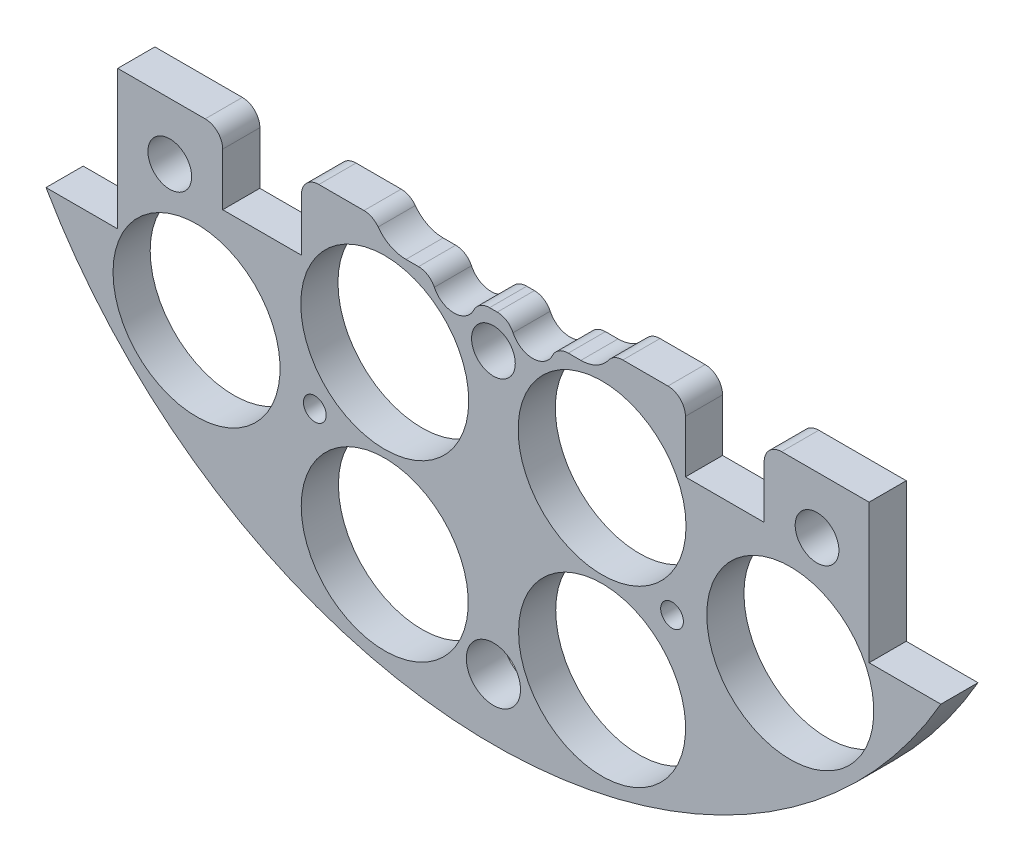
SolidWorks part; units mm, degrees
ref_plane "Front Plane" through (0, 0, 0) normal (0, 0, 1) x (1, 0, 0)
ref_plane "Top Plane" through (0, 0, 0) normal (0, 1, 0) x (1, 0, 0)
ref_plane "Right Plane" through (0, 0, 0) normal (1, 0, 0) x (0, 0, -1)
sketch "Sketch1" plane through (0, 0, 0) normal (0, 0, 1) x (1, 0, 0)
  line L0 (0, 0) -> (-82.1241, 0) construction
  line L1 (0, 0) -> (0, 95.6219) construction
  line L3 (-64.9644, 37.338) -> (-54.5504, 37.338)
  line L5 (-64.9644, -37.338) -> (-54.5504, -37.338)
  line L6 (-54.5504, 37.338) -> (-54.5504, -37.338)
  line L7 (64.9644, -37.338) -> (54.5504, -37.338)
  line L8 (64.9644, 37.338) -> (54.5504, 37.338)
  line L9 (54.5504, 37.338) -> (54.5504, -37.338)
  arc A0 (-64.9644, -37.338) -> (64.9644, -37.338) centre (0, 0) ccw
  circle A1 centre (-46.482, 11.049) radius 1.651
  circle A2 centre (-21.0833, 10.795) radius 1.651
  circle A3 centre (-21.0833, -10.795) radius 1.651
  circle A4 centre (-46.482, -11.049) radius 1.651
  circle A5 centre (46.482, -11.049) radius 1.651
  circle A6 centre (21.0833, -10.795) radius 1.651
  circle A7 centre (21.0833, 10.795) radius 1.651
  circle A8 centre (46.482, 11.049) radius 1.651
  arc A9 (64.9644, 37.338) -> (-64.9644, 37.338) centre (0, 0) ccw
  dimension "D2" = 3.302
  dimension "D3" = 3.302
  dimension "D4" = 25.4
  dimension "D5" = 10.795
  dimension "D10" = 46.482
  dimension "D6" = 74.676
  dimension "D7" = 10.414
  dimension "D8" = 74.93
  dimension "D9" = 74.93
  dimension "D11" = 37.338
extrude "Boss-Extrude2" add sketch "Sketch1" along normal blind 5.3975
sketch "Sketch2" plane through (0, 0, 5.3975) normal (0, 0, 1) x (1, 0, 0)
  line L0 (0, 68.58) -> (0, 55.88) construction
  line L1 (-9.525, 68.58) -> (9.525, 68.58)
  line L2 (-9.525, 68.58) -> (-9.525, 55.88)
  line L3 (-9.525, 55.88) -> (9.525, 55.88)
  line L4 (9.525, 68.58) -> (9.525, 55.88)
  line L5 (-9.525, 62.23) -> (9.525, 62.23) construction
  arc A0 (64.9644, 37.338) -> (-64.9644, 37.338) centre (0, 0) ccw construction
  circle A1 centre (-21.0833, 10.795) radius 1.651 construction
  circle A2 centre (21.0833, 10.795) radius 1.651 construction
  circle A3 centre (-6.731, 62.23) radius 1.143
  circle A4 centre (6.731, 62.23) radius 1.143
  dimension "D4" = 2.286
  dimension "D5" = 0
  dimension "D6" = 6.731
  dimension "D1" = 19.05
  dimension "D2" = 12.7
  dimension "D3" = 55.88
extrude "Cut-Extrude1" cut sketch "Sketch2" against normal through all contours A3 | A4
sketch "Sketch3" plane through (0, 0, 0) normal (0, 0, -1) x (-1, 0, 0)
  line L0 (0, 0) -> (0, -116.2908) construction
  line L1 (0, 0) -> (-153.8039, 0) construction
  line L2 (0, 0) -> (15.2681, -56.9814) construction
  line L3 (0, 0) -> (15.2302, -26.3795) construction
  circle A0 centre (-15.7776, -58.8828) radius 12.1285
  circle A3 centre (15.7776, -58.8828) radius 12.1285
  circle A4 centre (-43.1052, -43.1052) radius 12.1285
  circle A8 centre (-43.1052, 43.1052) radius 12.1285
  circle A11 centre (43.1052, 43.1052) radius 12.1285
  circle A14 centre (43.1052, -43.1052) radius 12.1285
  circle A33 centre (58.8828, -15.7776) radius 12.1285 [skipped]
  circle A34 centre (58.8828, 15.7776) radius 12.1285 [skipped]
  circle A35 centre (-58.8828, 15.7776) radius 12.1285 [skipped]
  circle A36 centre (-58.8828, -15.7776) radius 12.1285 [skipped]
  circle A37 centre (-15.7776, 58.8828) radius 12.1285 [skipped]
  circle A38 centre (15.7776, 58.8828) radius 12.1285 [skipped]
  point P36 (0, 0)
  point P53 (0, 0)
  point P55 (0, 0)
  dimension "D3" = 0
  dimension "D4" = 15
  dimension "D5" = 24.257
  dimension "D7" = 12
  dimension "D9" = 30
extrude "Cut-Extrude2" cut sketch "Sketch3" against normal through all
sketch "Sketch4" plane through (0, 0, 0) normal (0, 0, -1) x (-1, 0, 0)
  line L1 (-15.7702, 56.3138) -> (12.7925, 56.3138)
  line L2 (-15.7702, 56.3138) -> (-15.7702, 67.9913)
  line L3 (-15.7702, 67.9913) -> (12.7925, 67.9913)
  line L4 (12.7925, 56.3138) -> (12.7925, 67.9913)
extrude "Boss-Extrude3" add sketch "Sketch4" against normal up to surface (5.3975 mm away) up to face at (-55.2337, -43.1052, 5.3975)
sketch "Sketch5" plane through (0, 0, 0) normal (0, 0, -1) x (-1, 0, 0)
  line L1 (-85.044, -17.145) -> (131.6774, -17.145)
  line L2 (-85.044, -17.145) -> (-85.044, 113.4242)
  line L3 (-85.044, 113.4242) -> (131.6774, 113.4242)
  line L4 (131.6774, -17.145) -> (131.6774, 113.4242)
  circle A0 centre (-21.0833, -10.795) radius 1.651 construction
  dimension "D1" = 6.35
extrude "Cut-Extrude4" cut sketch "Sketch5" against normal through all contours L2 L3 L4 L1
extrude "Cut-Extrude5" cut sketch "Sketch6" against normal through all both and the other way through all
sketch "Sketch6" plane through (31.3134, 132.614, -3.175) normal (0, 0, -1) x (0, 1, 0)
  line L0 (-132.614, -31.3134) -> (-132.614, 57.8454) construction
  line L1 (-132.614, -31.3134) -> (-222.516, -31.3134) construction
  circle A0 centre (-158.014, 14.4066) radius 3.175
  circle A1 centre (-173.254, -31.3134) radius 3.175
  circle A3 centre (-158.014, -77.0334) radius 3.175
  circle A4 centre (-107.214, -77.0334) radius 3.175
  circle A5 centre (-91.974, -31.3134) radius 3.175
  circle A6 centre (-107.214, 14.4066) radius 3.175
extrude "Cut-Extrude7" cut sketch "Sketch8" against normal blind 29.21
sketch "Sketch8" plane through (31.3134, 132.559, 0) normal (0, 0, -1) x (0, 1, 0)
  line L0 (-132.559, -31.3134) -> (6.1626, -31.3134) construction
  line L2 (-132.559, -31.3134) -> (-132.559, -122.6589) construction
  circle A0 centre (-190.979, 2.9766) radius 1.651
  circle A2 centre (-154.784, -31.3134) radius 1.651
  circle A3 centre (-190.979, -65.6034) radius 1.651
  circle A4 centre (-110.334, -31.3134) radius 1.651
  circle A5 centre (-74.139, -65.6034) radius 1.651
  circle A6 centre (-74.139, 2.9766) radius 1.651
sketch "Sketch11" plane through (0, 0, 0) normal (0, 0, -1) x (-1, 0, 0)
  line L0 (-54.5504, -17.145) -> (54.5504, -17.145) construction
  circle A0 centre (0, -66.045) radius 3.937
  point P4 (0, -17.145)
  dimension "D1" = 7.874
  dimension "D2" = 48.9
extrude "Cut-Extrude11" cut sketch "Sketch11" against normal through all
sketch "Sketch12" plane through (0, 0, 0) normal (0, 0, -1) x (-1, 0, 0)
  line L0 (-54.5504, -17.145) -> (54.5504, -17.145) construction
  line L1 (-39.3104, -17.145) -> (-27.8804, -17.145)
  line L2 (-39.3104, -17.145) -> (-39.3104, -27.305)
  line L3 (-39.3104, -27.305) -> (-27.8804, -27.305)
  line L4 (-27.8804, -17.145) -> (-27.8804, -27.305)
  line L5 (-54.5504, -37.338) -> (-54.5504, -17.145) construction
  line L6 (27.8804, -17.145) -> (39.3104, -17.145)
  line L7 (27.8804, -17.145) -> (27.8804, -27.305)
  line L8 (27.8804, -27.305) -> (39.3104, -27.305)
  line L9 (39.3104, -17.145) -> (39.3104, -27.305)
  line L10 (0, -10.2409) -> (0, -88.0539) construction
  dimension "D1" = 15.24
  dimension "D2" = 11.43
  dimension "D3" = 10.16
extrude "Cut-Extrude12" cut sketch "Sketch12" against normal through all
sketch "Sketch16" plane through (0, 0, 0) normal (0, 0, -1) x (-1, 0, 0)
  line L0 (0, 0) -> (0, 27.5884) construction
  circle A0 centre (15.7776, -33.4828) radius 12.192
  circle A2 centre (15.7776, -58.8828) radius 12.1285 construction
  circle A3 centre (-15.7776, -33.4828) radius 12.192
  dimension "D1" = 24.384
  dimension "D2" = 25.4
  dimension "D3" = 0
extrude "Cut-Extrude16" cut sketch "Sketch16" against normal blind 21.59
sketch "Sketch57" plane through (0, 0, 0) normal (0, 0, -1) x (-1, 0, 0)
  line L0 (0, 0) -> (0, -110.6636) construction
  circle A0 centre (-25.9376, -45.6452) radius 1.651
  circle A1 centre (-43.1052, -43.1052) radius 12.1285 construction
  circle A2 centre (-15.7776, -33.4828) radius 12.192 construction
  circle A3 centre (25.9376, -45.6452) radius 1.651
  dimension "D1" = 3.302
  dimension "D2" = 2.54
  dimension "D3" = 10.16
extrude "Cut-Extrude57" cut sketch "Sketch57" against normal blind 58.674
extrude "Cut-Extrude58" cut sketch "Sketch58" against normal blind 48.768 and the other way blind 103.378
sketch "Sketch58" plane through (30.092, 4.0835, 36.1315) normal (0, 0, -1) x (-1, 0, 0)
  line L0 (30.092, -4.0835) -> (148.6336, -4.0835) construction
  line L1 (30.092, -4.0835) -> (30.092, 90.452) construction
  circle A0 centre (-16.898, 21.3165) radius 3.175
  circle A1 centre (77.082, 21.3165) radius 3.175
  circle A2 centre (30.092, 21.3165) radius 3.175
  circle A4 centre (77.082, -29.4835) radius 3.175
  circle A5 centre (30.092, -29.4835) radius 3.175
  circle A6 centre (-16.898, -29.4835) radius 3.175
sketch "Sketch15" plane through (0, 0, 0) normal (0, 0, -1) x (-1, 0, 0)
  line L0 (0, 0) -> (0, 42.4042) construction
  line L1 (-12.7, -20.24) -> (-8.889, -20.24)
  line L2 (-2.541, -20.24) -> (2.541, -20.24)
  line L3 (-1.06, -15.24) -> (7.7, -15.24)
  line L4 (8.889, -20.24) -> (12.7, -20.24)
  arc A0 (-9.38, -11.5013) -> (-12.7, -20.24) centre (-12.7, -15.24) ccw
  arc A1 (7.7, -15.24) -> (12.7, -20.24) centre (12.7, -15.24) cw
  arc A2 (-1.06, -15.24) -> (-9.38, -11.5013) centre (-6.06, -15.24) ccw
  arc A3 (-8.889, -20.24) -> (-2.541, -20.24) centre (-5.715, -20.32) ccw
  arc A4 (2.541, -20.24) -> (8.889, -20.24) centre (5.715, -20.32) ccw
  dimension "D1" = 10
  dimension "D4" = 6.35
  dimension "D6" = 6.35
  dimension "D2" = 15.24
  dimension "D3" = 12.7
  dimension "D5" = 6.64
  dimension "D7" = 11.43
  dimension "D8" = 5.715
  dimension "D9" = 20.32
extrude "Cut-Extrude15" cut sketch "Sketch15" against normal blind 21.59
fillet "Fillet1" radius 2.54 10 edges at (-27.8804, -17.145, 2.6987) (-39.3104, -17.145, 2.6987) (-17.3229, -17.145, 2.6987) (-8.889, -20.24, 2.6987) (-2.541, -20.24, 2.6987) (2.541, -20.24, 2.6987) (8.889, -20.24, 2.6987) (17.3229, -17.145, 2.6987) (27.8804, -17.145, 2.6987) (39.3104, -17.145, 2.6987)
